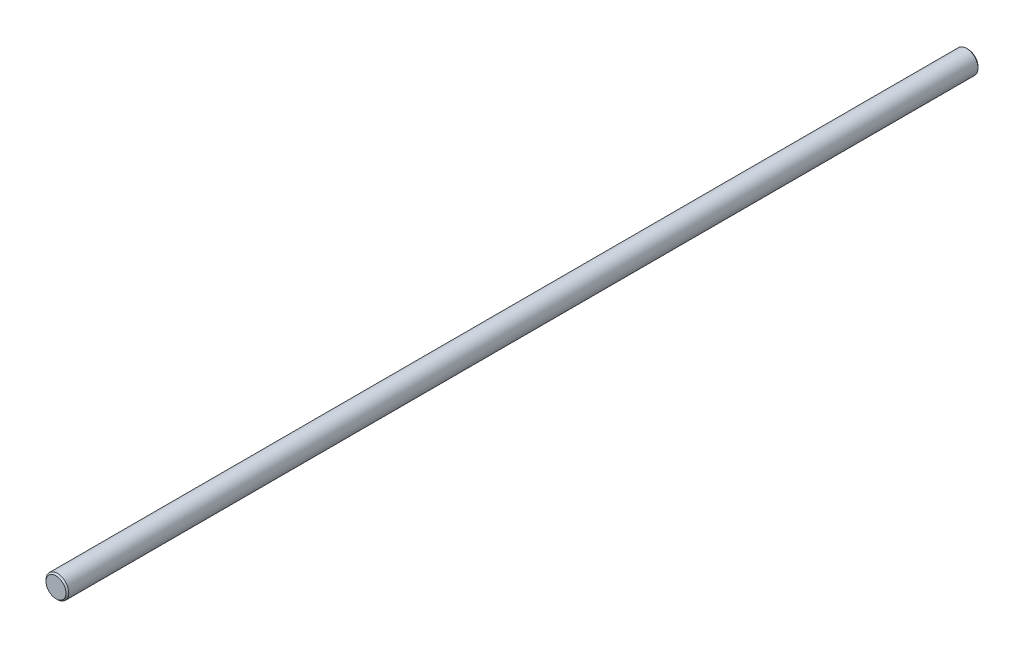
SolidWorks part; units mm, degrees
material "AISI 304"
ref_plane "Front Plane" through (0, 0, 0) normal (0, 0, 1) x (1, 0, 0)
ref_plane "Top Plane" through (0, 0, 0) normal (0, 1, 0) x (1, 0, 0)
ref_plane "Right Plane" through (0, 0, 0) normal (1, 0, 0) x (0, 0, -1)
sketch "Sketch1" plane through (0, 0, 0) normal (0, 0, 1) x (1, 0, 0)
  circle A0 centre (0, 0) radius 4
  dimension "D1" = 8
extrude "Boss-Extrude1" add sketch "Sketch1" against normal blind 320
chamfer "Chamfer1" distance 0.5 angle 45 2 edges at (4, 0, -320) (4, 0, 0)
